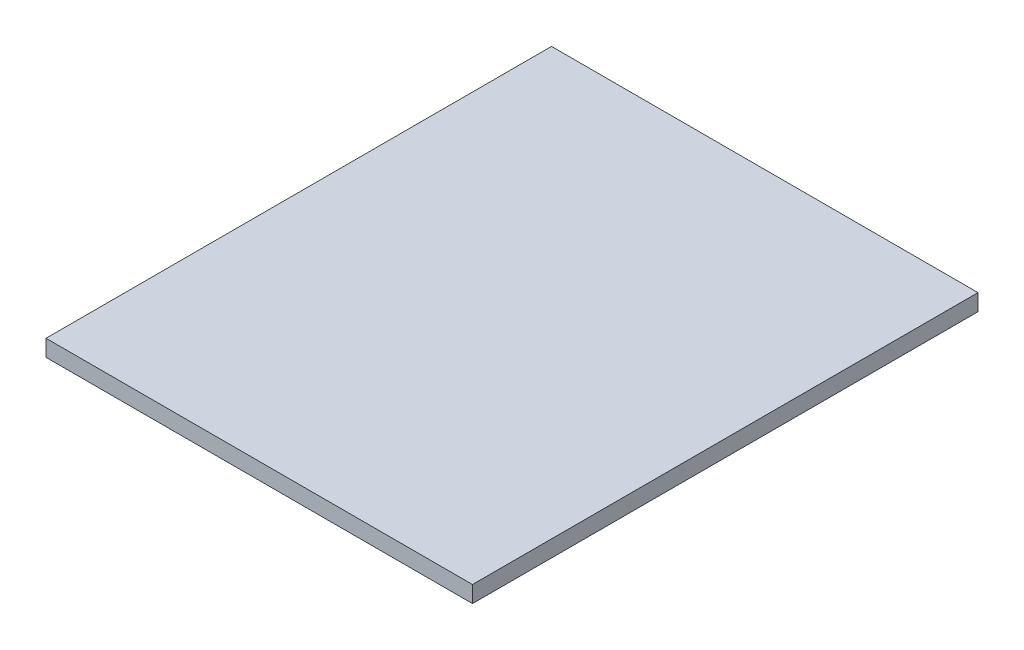
SolidWorks part; units mm, degrees
ref_plane "Спереди" through (0, 0, 0) normal (0, 0, 1) x (1, 0, 0)
ref_plane "Сверху" through (0, 0, 0) normal (0, 1, 0) x (1, 0, 0)
ref_plane "Справа" through (0, 0, 0) normal (1, 0, 0) x (0, 0, -1)
sketch "Эскиз1" plane through (0, 0, 0) normal (0, 1, 0) x (1, 0, 0)
  line L1 (232, -275) -> (-232, -275)
  line L2 (232, -275) -> (232, 275)
  line L3 (232, 275) -> (-232, 275)
  line L4 (-232, -275) -> (-232, 275)
  line L5 (232, -275) -> (-232, 275) construction
  line L6 (232, 275) -> (-232, -275) construction
  point P0 (0, 0)
  dimension "D1" = 464
  dimension "D2" = 550
extrude "Бобышка-Вытянуть1" add sketch "Эскиз1" along normal blind 18
